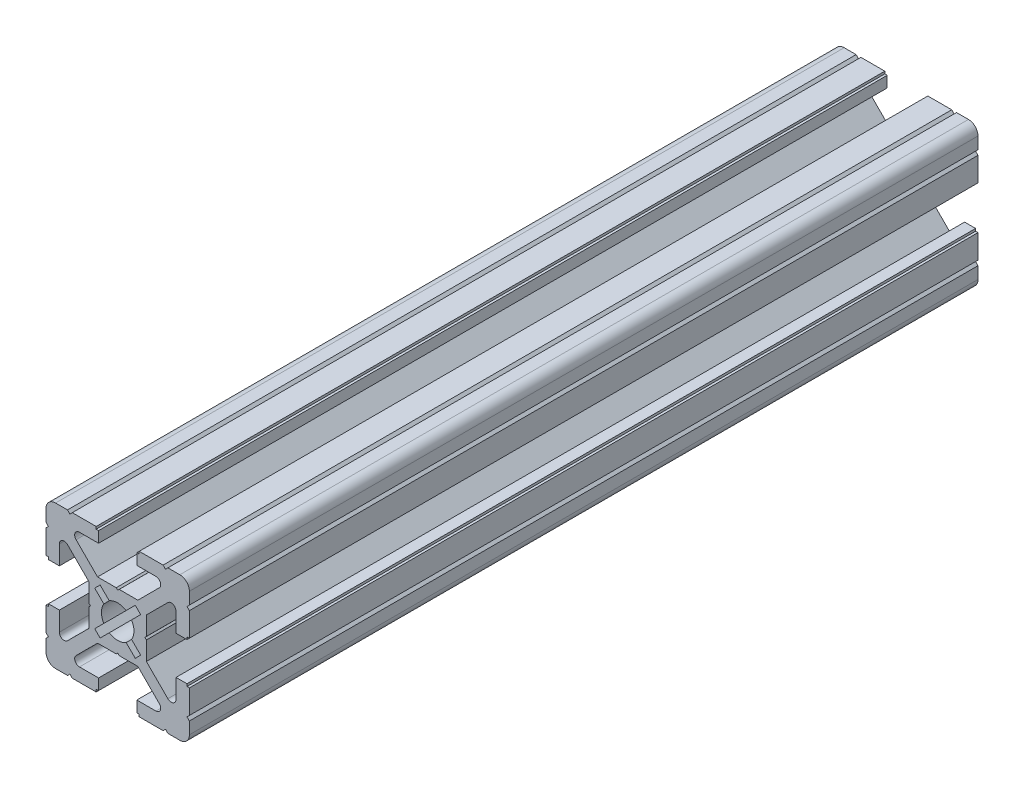
SolidWorks part; units mm, degrees
ref_plane "Front Plane" through (0, 0, 0) normal (0, 0, 1) x (1, 0, 0)
ref_plane "Top Plane" through (0, 0, 0) normal (0, 1, 0) x (1, 0, 0)
ref_plane "Right Plane" through (0, 0, 0) normal (1, 0, 0) x (0, 0, -1)
ref_plane "Plane1" through (0, 0, -65) normal (0, 0, -1) x (-1, 0, 0)
sketch "Sketch1" plane through (0, 0, -65) normal (0, 0, -1) x (-1, 0, 0)
  line L0 (4.8083, 3.677) -> (2.9023, 1.771)
  line L1 (2.9023, -1.771) -> (4.8083, -3.677)
  line L2 (4.8083, -3.677) -> (3.677, -4.8083)
  line L3 (3.677, -4.8083) -> (1.771, -2.9023)
  line L4 (-1.771, -2.9023) -> (-3.677, -4.8083)
  line L5 (-3.677, -4.8083) -> (-4.8083, -3.677)
  line L6 (-4.8083, -3.677) -> (-2.9023, -1.771)
  line L7 (-2.9023, 1.771) -> (-4.8083, 3.677)
  line L8 (-4.8083, 3.677) -> (-3.677, 4.8083)
  line L9 (-3.677, 4.8083) -> (-1.771, 2.9023)
  line L10 (1.771, 2.9023) -> (3.677, 4.8083)
  line L11 (3.677, 4.8083) -> (4.8083, 3.677)
  line L12 (-15, 13) -> (-15, 10.5)
  line L13 (-15, 10.5) -> (-14.5, 10)
  line L14 (-14.5, 10) -> (-15, 9.5)
  line L15 (-15, 9.5) -> (-15, 4.5)
  line L16 (-15, 4.5) -> (-14.5, 4.5)
  line L17 (-14.5, 4.5) -> (-14.5, 4)
  line L18 (-14.5, 4) -> (-12.2, 4)
  line L19 (-12.2, 4) -> (-12.2, 8)
  line L20 (-10.4929, 8.7071) -> (-6, 4.2142)
  line L21 (-6, 4.2142) -> (-6, 0.3125)
  line L22 (-6, 0.3125) -> (-5.7, 0)
  line L23 (-5.7, 0) -> (-6, -0.3125)
  line L24 (-6, -0.3125) -> (-6, -4.2142)
  line L25 (-6, -4.2142) -> (-10.4929, -8.7071)
  line L26 (-12.2, -8) -> (-12.2, -4)
  line L27 (-12.2, -4) -> (-14.5, -4)
  line L28 (-14.5, -4) -> (-14.5, -4.5)
  line L29 (-14.5, -4.5) -> (-15, -4.5)
  line L30 (-15, -4.5) -> (-15, -9.5)
  line L31 (-15, -9.5) -> (-14.5, -10)
  line L32 (-14.5, -10) -> (-15, -10.5)
  line L33 (-15, -10.5) -> (-15, -13)
  line L34 (-13, -15) -> (-10.5, -15)
  line L35 (-10.5, -15) -> (-10, -14.5)
  line L36 (-10, -14.5) -> (-9.5, -15)
  line L37 (-9.5, -15) -> (-4.5, -15)
  line L38 (-4.5, -15) -> (-4.5, -14.5)
  line L39 (-4.5, -14.5) -> (-4, -14.5)
  line L40 (-4, -14.5) -> (-4, -12.2)
  line L41 (-4, -12.2) -> (-8, -12.2)
  line L42 (-8.7071, -10.4929) -> (-4.2142, -6)
  line L43 (-4.2142, -6) -> (-0.3125, -6)
  line L44 (-0.3125, -6) -> (0, -5.7)
  line L45 (0, -5.7) -> (0.3125, -6)
  line L46 (0.3125, -6) -> (4.2142, -6)
  line L47 (4.2142, -6) -> (8.7071, -10.4929)
  line L48 (8, -12.2) -> (4, -12.2)
  line L49 (4, -12.2) -> (4, -14.5)
  line L50 (4, -14.5) -> (4.5, -14.5)
  line L51 (4.5, -14.5) -> (4.5, -15)
  line L52 (4.5, -15) -> (9.5, -15)
  line L53 (9.5, -15) -> (9.9899, -14.5)
  line L54 (9.9899, -14.5) -> (10.4899, -15)
  line L55 (10.4899, -15) -> (13, -15)
  line L56 (15, -13) -> (15, -10.5)
  line L57 (15, -10.5) -> (14.5, -10)
  line L58 (14.5, -10) -> (15, -9.5)
  line L59 (15, -9.5) -> (15, -4.5)
  line L60 (15, -4.5) -> (14.5, -4.5)
  line L61 (14.5, -4.5) -> (14.5, -4)
  line L62 (14.5, -4) -> (12.2, -4)
  line L63 (12.2, -4) -> (12.2, -8)
  line L64 (10.4929, -8.7071) -> (6, -4.2142)
  line L65 (6, -4.2142) -> (6, -0.3125)
  line L66 (6, -0.3125) -> (5.7, 0)
  line L67 (5.7, 0) -> (6, 0.3125)
  line L68 (6, 0.3125) -> (6, 4.2142)
  line L69 (6, 4.2142) -> (10.4929, 8.7071)
  line L70 (12.2, 8) -> (12.2, 4)
  line L71 (12.2, 4) -> (14.5, 4)
  line L72 (14.5, 4) -> (14.5, 4.5)
  line L73 (14.5, 4.5) -> (15, 4.5)
  line L74 (15, 4.5) -> (15, 9.5)
  line L75 (15, 9.5) -> (14.5, 10)
  line L76 (14.5, 10) -> (15, 10.5)
  line L77 (15, 10.5) -> (15, 13)
  line L78 (13, 15) -> (10.5, 15)
  line L79 (10.5, 15) -> (10, 14.5)
  line L80 (10, 14.5) -> (9.5, 15)
  line L81 (9.5, 15) -> (4.5, 15)
  line L82 (4.5, 15) -> (4.5, 14.5)
  line L83 (4.5, 14.5) -> (4, 14.5)
  line L84 (4, 14.5) -> (4, 12.2)
  line L85 (4, 12.2) -> (8, 12.2)
  line L86 (8.7071, 10.4929) -> (4.2142, 6)
  line L87 (4.2142, 6) -> (0.3125, 6)
  line L88 (0.3125, 6) -> (0, 5.7)
  line L89 (0, 5.7) -> (-0.3125, 6)
  line L90 (-0.3125, 6) -> (-4.2142, 6)
  line L91 (-4.2142, 6) -> (-8.7071, 10.4929)
  line L92 (-8, 12.2) -> (-4, 12.2)
  line L93 (-4, 12.2) -> (-4, 14.5)
  line L94 (-4, 14.5) -> (-4.5, 14.5)
  line L95 (-4.5, 14.5) -> (-4.5, 15)
  line L96 (-4.5, 15) -> (-9.5, 15)
  line L97 (-9.5, 15) -> (-10, 14.5)
  line L98 (-10, 14.5) -> (-10.5, 15)
  line L99 (-10.5, 15) -> (-13, 15)
  arc A0 (2.9023, 1.771) -> (2.9023, -1.771) centre (0, 0) cw
  arc A1 (1.771, -2.9023) -> (-1.771, -2.9023) centre (0, 0) cw
  arc A2 (-2.9023, -1.771) -> (-2.9023, 1.771) centre (0, 0) cw
  arc A3 (-1.771, 2.9023) -> (1.771, 2.9023) centre (0, 0) cw
  arc A4 (-13, 15) -> (-15, 13) centre (-13, 13) ccw
  arc A5 (-12.2, 8) -> (-10.4929, 8.7071) centre (-11.2, 8) cw
  arc A6 (-10.4929, -8.7071) -> (-12.2, -8) centre (-11.2, -8) cw
  arc A7 (-15, -13) -> (-13, -15) centre (-13, -13) ccw
  arc A8 (-8, -12.2) -> (-8.7071, -10.4929) centre (-8, -11.2) cw
  arc A9 (8.7071, -10.4929) -> (8, -12.2) centre (8, -11.2) cw
  arc A10 (13, -15) -> (15, -13) centre (13, -13) ccw
  arc A11 (12.2, -8) -> (10.4929, -8.7071) centre (11.2, -8) cw
  arc A12 (10.4929, 8.7071) -> (12.2, 8) centre (11.2, 8) cw
  arc A13 (15, 13) -> (13, 15) centre (13, 13) ccw
  arc A14 (8, 12.2) -> (8.7071, 10.4929) centre (8, 11.2) cw
  arc A15 (-8.7071, 10.4929) -> (-8, 12.2) centre (-8, 11.2) cw
extrude "Boss-Extrude1" add sketch "Sketch1" against normal blind 165
ref_plane "Plane2" through (0, 0, 17.5) normal (0, 0, 1) x (1, 0, 0)
